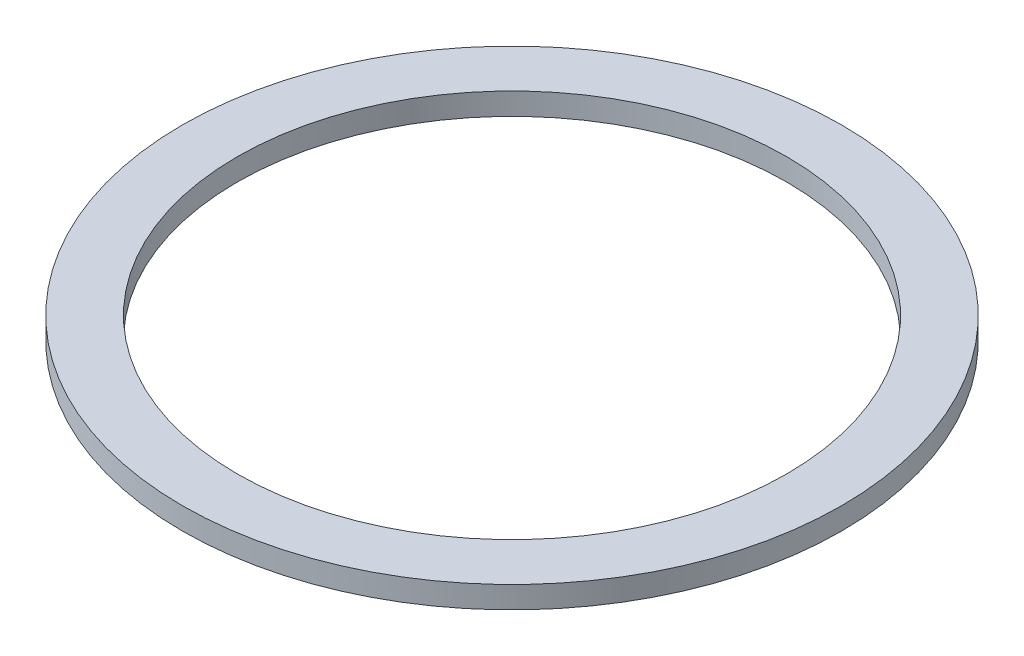
SolidWorks part; units mm, degrees
ref_plane "Спереди" through (0, 0, 0) normal (0, 0, 1) x (1, 0, 0)
ref_plane "Сверху" through (0, 0, 0) normal (0, 1, 0) x (1, 0, 0)
ref_plane "Справа" through (0, 0, 0) normal (1, 0, 0) x (0, 0, -1)
sketch "Эскиз2" plane through (0, 0, 0) normal (0, 0, 1) x (1, 0, 0)
  line L0 (0, 22.758) -> (0, -22.758) construction
  line L1 (-55.1101, 0) -> (57.7875, 0) construction
  line L2 (27.5, 0) -> (27.5, -0.5) construction
  line L3 (25, 0) -> (30, 0)
  line L4 (25, 0) -> (25, 2)
  line L5 (25, 2) -> (30, 2)
  line L6 (30, 0) -> (30, 2)
  circle A0 centre (27.5, -0.5) radius 1.5
  dimension "D4" = 3
  dimension "D1" = 25
  dimension "D2" = 30
  dimension "D3" = 2
  dimension "D5" = 0.5
revolve "Повернуть1" add sketch "Эскиз2" angle 360 about L0
